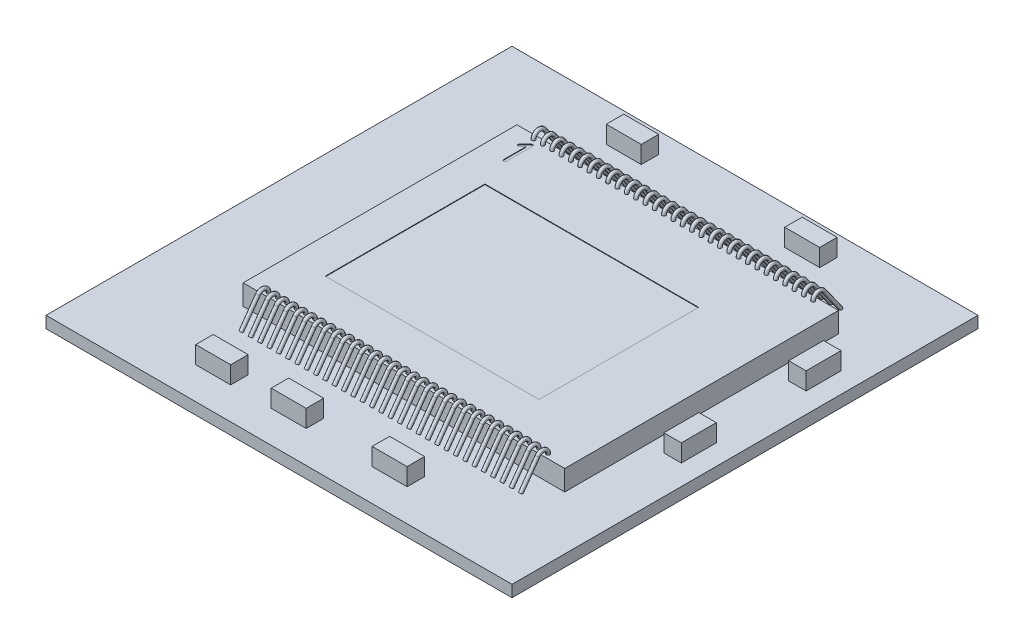
SolidWorks part; units mm, degrees
material "1060 Legierung"
ref_plane "Vorne" through (0, 0, 0) normal (0, 0, 1) x (1, 0, 0)
ref_plane "Oben" through (0, 0, 0) normal (0, 1, 0) x (1, 0, 0)
ref_plane "Rechts" through (0, 0, 0) normal (1, 0, 0) x (0, 0, -1)
ref_plane "Faser-Ebene_Vorne" through (0, 0, 0.175) normal (0, 0, 1) x (1, 0, 0)
ref_plane "Faser-Ebene_Rechts" through (-0.32, 0, 0) normal (1, 0, 0) x (0, 0, -1)
sketch "X-Ray_side"
sketch "Chip_Dimensions"
sketch "Skizze1" plane through (0, 0, 0) normal (0, 1, 0) x (1, 0, 0)
  line L0 (-2.76, 2.35) -> (2.76, -2.35) construction
  line L1 (-2.76, 2.35) -> (2.76, 2.35)
  line L2 (-2.76, 2.35) -> (-2.76, -2.35)
  line L3 (-2.76, -2.35) -> (2.76, -2.35)
  line L4 (2.76, 2.35) -> (2.76, -2.35)
  dimension "D1" = 5.52
  dimension "D2" = 4.7
extrude "Chip_Die" add sketch "Skizze1" along normal blind 0.35
sketch "Skizze4" plane through (0, 0.35, 0) normal (0, 1, 0) x (1, 0, 0)
  line L1 (-2.155, 1.195) -> (1.515, 1.195)
  line L2 (-2.155, 1.195) -> (-2.155, -1.545)
  line L3 (-2.155, -1.545) -> (1.515, -1.545)
  line L4 (1.515, 1.195) -> (1.515, -1.545)
  line L5 (-0.32, 1.195) -> (-0.32, -0.1113) construction
  line L7 (-0.32, -0.1925) -> (-0.32, 0.1925) construction
  line L8 (1.515, -0.175) -> (0.7734, -0.175) construction
  line L9 (-0.1925, -0.175) -> (0.1925, -0.175) construction
  dimension "D1" = 3.67
  dimension "D2" = 2.74
extrude "Active_Area" cut sketch "Skizze4" against normal blind 0.01
sketch "Skizze5" plane through (0, 0.35, 0) normal (0, 1, 0) x (1, 0, 0)
  text T0 "1" font "ISOCPEUR" height 0.5
extrude "Pin1" cut sketch "Skizze5" against normal blind 0.01
sketch "Skizze6" plane through (0, 0, 0) normal (0, 1, 0) x (1, 0, 0)
  line L0 (-2.155, 1.195) -> (1.515, -1.545) construction
  line L1 (-4.32, 3.825) -> (3.68, 3.825)
  line L2 (-4.32, 3.825) -> (-4.32, -4.175)
  line L3 (-4.32, -4.175) -> (3.68, -4.175)
  line L4 (3.68, 3.825) -> (3.68, -4.175)
  line L5 (3.68, 3.825) -> (-4.32, -4.175) construction
  point P7 (-0.32, -0.175)
  dimension "D1" = 8
extrude "Base-Plate" add sketch "Skizze6" against normal blind 0.2
sketch "Skizze12" plane through (0, 0, 0) normal (1, 0, 0) x (0, 0, -1)
  line L0 (-2.35, 0.35) -> (2.35, 0.35) construction
  line L1 (-2.4563, 0.4079) -> (-2.7458, 0)
  line L2 (-4.175, 0) -> (3.825, 0) construction
  line L3 (0, 0) -> (0, 1.1196) construction
  arc A0 (-2.2748, 0.35) -> (-2.4563, 0.4079) centre (-2.3748, 0.35) ccw
  dimension "D1" = 0.1
sketch "Skizze13" plane through (0, 0.35, 0) normal (0, 1, 0) x (1, 0, 0)
  line L0 (0, 0) -> (0, -1.1473) construction
  circle A0 centre (0, -2.2748) radius 0.03
  circle A1 centre (0.16, -2.2748) radius 0.03
  circle A2 centre (0.32, -2.2748) radius 0.03
  circle A3 centre (0.48, -2.2748) radius 0.03
  circle A4 centre (0.64, -2.2748) radius 0.03
  circle A5 centre (0.8, -2.2748) radius 0.03
  circle A6 centre (0.96, -2.2748) radius 0.03
  circle A7 centre (1.12, -2.2748) radius 0.03
  circle A8 centre (1.28, -2.2748) radius 0.03
  circle A9 centre (1.44, -2.2748) radius 0.03
  circle A10 centre (1.6, -2.2748) radius 0.03
  circle A11 centre (1.76, -2.2748) radius 0.03
  circle A12 centre (1.92, -2.2748) radius 0.03
  circle A13 centre (2.08, -2.2748) radius 0.03
  circle A14 centre (2.24, -2.2748) radius 0.03
  circle A15 centre (2.4, -2.2748) radius 0.03
  circle A16 centre (-2.4, -2.2748) radius 0.03
  circle A17 centre (-2.24, -2.2748) radius 0.03
  circle A18 centre (-2.08, -2.2748) radius 0.03
  circle A19 centre (-1.92, -2.2748) radius 0.03
  circle A20 centre (-1.76, -2.2748) radius 0.03
  circle A21 centre (-1.6, -2.2748) radius 0.03
  circle A22 centre (-1.44, -2.2748) radius 0.03
  circle A23 centre (-1.28, -2.2748) radius 0.03
  circle A24 centre (-1.12, -2.2748) radius 0.03
  circle A25 centre (-0.96, -2.2748) radius 0.03
  circle A26 centre (-0.8, -2.2748) radius 0.03
  circle A27 centre (-0.64, -2.2748) radius 0.03
  circle A28 centre (-0.48, -2.2748) radius 0.03
  circle A29 centre (-0.32, -2.2748) radius 0.03
  circle A30 centre (-0.16, -2.2748) radius 0.03
  dimension "D1" = 0.06
  dimension "D2" = 16
sweep "Bonding-wires" add profiles "Skizze13" path "Skizze12"
mirror "Spiegeln1" about plane through (0, 0, 0) normal (0, 0, 1) of "Bonding-wires"
sketch "X-Ray_top"
sketch "Skizze14" plane through (0, 0, 0) normal (0, 1, 0) x (1, 0, 0)
  line L0 (-4.32, -4.175) -> (3.68, -4.175) construction
  line L1 (-2.2994, -3.325) -> (-1.6994, -3.325)
  line L2 (-2.2994, -3.325) -> (-2.2994, -3.625)
  line L3 (-2.2994, -3.625) -> (-1.6994, -3.625)
  line L4 (-1.6994, -3.325) -> (-1.6994, -3.625)
  line L5 (3.68, -4.175) -> (3.68, 3.825) construction
  line L6 (-1.0036, -3.325) -> (-0.4036, -3.325)
  line L7 (-1.0036, -3.325) -> (-1.0036, -3.625)
  line L8 (-1.0036, -3.625) -> (-0.4036, -3.625)
  line L9 (-0.4036, -3.325) -> (-0.4036, -3.625)
  line L10 (0.7291, -3.625) -> (1.3291, -3.625)
  line L11 (0.7291, -3.625) -> (0.7291, -3.325)
  line L12 (0.7291, -3.325) -> (1.3291, -3.325)
  line L13 (1.3291, -3.625) -> (1.3291, -3.325)
  line L14 (3.03, -0.3181) -> (3.33, -0.3181)
  line L15 (3.03, -0.3181) -> (3.03, -0.9181)
  line L16 (3.03, -0.9181) -> (3.33, -0.9181)
  line L17 (3.33, -0.3181) -> (3.33, -0.9181)
  line L18 (3.68, 3.825) -> (-4.32, 3.825) construction
  line L19 (3.03, 1.2236) -> (3.33, 1.2236)
  line L20 (3.03, 1.2236) -> (3.03, 1.8236)
  line L21 (3.03, 1.8236) -> (3.33, 1.8236)
  line L22 (3.33, 1.2236) -> (3.33, 1.8236)
  line L23 (-1.4515, 3.175) -> (-2.0515, 3.175)
  line L24 (-1.4515, 3.175) -> (-1.4515, 3.475)
  line L25 (-1.4515, 3.475) -> (-2.0515, 3.475)
  line L26 (-2.0515, 3.175) -> (-2.0515, 3.475)
  line L28 (1.012, 3.475) -> (1.612, 3.475)
  line L29 (1.012, 3.475) -> (1.012, 3.175)
  line L30 (1.012, 3.175) -> (1.612, 3.175)
  line L31 (1.612, 3.475) -> (1.612, 3.175)
  dimension "D1" = 0.3
  dimension "D2" = 0.6
  dimension "D3" = 0.55
  dimension "D4" = 0.35
  dimension "D5" = 0.35
extrude "Electronic_components" add sketch "Skizze14" along normal blind 0.3
